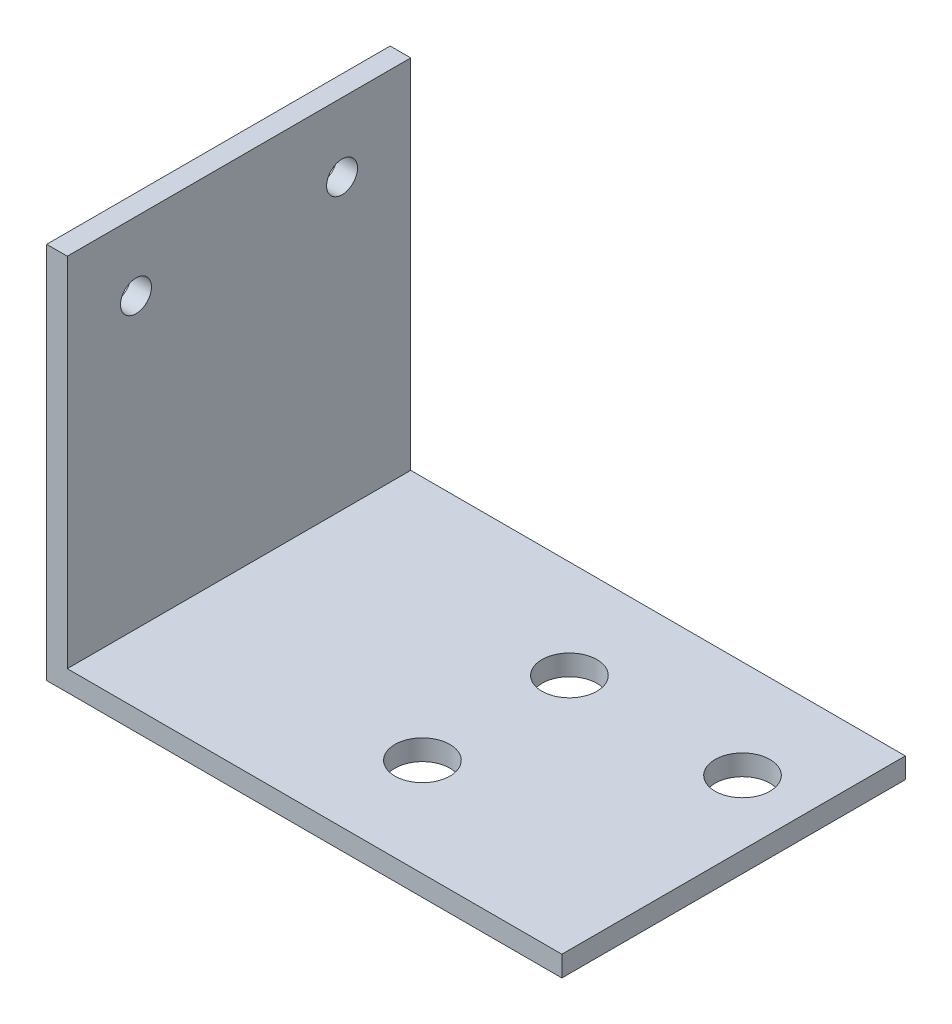
SolidWorks part; units mm, degrees
material "PBT Общее назначение"
ref_plane "Спереди" through (0, 0, 0) normal (0, 0, 1) x (1, 0, 0)
ref_plane "Сверху" through (0, 0, 0) normal (0, 1, 0) x (1, 0, 0)
ref_plane "Справа" through (0, 0, 0) normal (1, 0, 0) x (0, 0, -1)
sketch "Эскиз1" plane through (0, 0, 0) normal (0, 0, 1) x (1, 0, 0)
  line L0 (0, 0) -> (75, 0)
  line L1 (75, 0) -> (75, 3)
  line L2 (75, 3) -> (3, 3)
  line L3 (3, 3) -> (3, 55)
  line L4 (3, 55) -> (0, 55)
  line L5 (0, 55) -> (0, 0)
  dimension "D1" = 3
  dimension "D2" = 3
  dimension "D3" = 75
  dimension "D4" = 55
extrude "Бобышка-Вытянуть1" add sketch "Эскиз1" along normal blind 50
sketch "Эскиз2" plane through (0, 0, 0) normal (-1, 0, 0) x (0, 0, 1)
  line L0 (25, 55) -> (25, 0) construction
  line L1 (50, 55) -> (0, 55) construction
  line L2 (50, 0) -> (0, 0) construction
sketch "Эскиз3" plane through (0, 3, 0) normal (0, 1, 0) x (1, 0, 0)
  line L4 (66.75, -39.75) -> (66.75, -38.75)
  line L5 (66.75, -38.75) -> (39.25, -38.75)
  line L6 (39.25, -38.75) -> (39.25, -39.75)
  line L7 (39.25, -39.75) -> (66.75, -39.75)
  line L8 (66.75, -39.75) -> (66.75, -38.75)
  line L9 (66.75, -38.75) -> (39.25, -38.75)
  line L10 (39.25, -38.75) -> (39.25, -39.75)
  line L11 (39.25, -39.75) -> (66.75, -39.75)
  line L12 (66.75, -10.25) -> (39.25, -10.25)
  line L13 (66.75, -11.25) -> (66.75, -10.25)
  line L14 (39.25, -11.25) -> (66.75, -11.25)
  line L15 (39.25, -10.25) -> (39.25, -11.25)
  line L16 (66.75, -10.25) -> (39.25, -10.25)
  line L17 (66.75, -11.25) -> (66.75, -10.25)
  line L18 (39.25, -11.25) -> (66.75, -11.25)
  line L19 (39.25, -10.25) -> (39.25, -11.25)
  circle A0 centre (23, 25) radius 1.55 construction
  circle A1 centre (40.4, -35.7) radius 2
  circle A2 centre (40.4, -35.7) radius 2
  circle A3 centre (40.4, -14.3) radius 2
  circle A4 centre (40.4, -14.3) radius 2
  circle A7 centre (53, -32) radius 1
  circle A8 centre (53, -32) radius 1
  circle A9 centre (53, -18) radius 1
  circle A10 centre (53, -18) radius 1
  circle A11 centre (23, 25) radius 1.55
  circle A12 centre (23, -70) radius 1.55 construction
  circle A13 centre (23, -70) radius 1.55
  dimension "D1" = 0
  dimension "D2" = 0
  dimension "D4" = 0
  dimension "D5" = 0
  dimension "D6" = 0
  dimension "D7" = 0
sketch "Эскиз6" plane through (0, 3, 0) normal (0, 1, 0) x (1, 0, 0)
  circle A5 centre (40.4, -14.3) radius 2
  circle A6 centre (40.4, -14.3) radius 2
  circle A7 centre (40.4, -35.7) radius 2
  circle A8 centre (40.4, -35.7) radius 2
  dimension "D3" = 0
  dimension "D4" = 0
extrude "Вырез-Вытянуть2" cut sketch "Эскиз6" against normal through all
sketch "Sketch1" plane through (0, 3, 0) normal (0, 1, 0) x (1, 0, 0)
  circle A0 centre (65.6, -14.3) radius 2 construction
  circle A1 centre (65.6, -14.3) radius 2
extrude "Cut-Extrude1" cut sketch "Sketch1" against normal through all
sketch "Sketch2" plane through (0, 3, 0) normal (0, 1, 0) x (1, 0, 0)
  circle A0 centre (40.4, -14.3) radius 4
  circle A1 centre (65.6, -14.3) radius 4
  circle A2 centre (40.4, -35.7) radius 4
  dimension "D1" = 8
  dimension "D2" = 8
  dimension "D3" = 8
extrude "Cut-Extrude2" cut sketch "Sketch2" against normal through all
sketch "Sketch3" plane through (0, 3, 0) normal (0, 1, 0) x (1, 0, 0)
  line L0 (65.6, -14.3) -> (40.4, -14.3) construction
  line L1 (40.4, -14.3) -> (40.4, -35.7) construction
ref_plane "Отв вдоль" through (0, 0, 14.3) normal (0, 0, -1) x (-1, 0, 0)
ref_plane "Отв поп" through (40.4, 0, 0) normal (-1, 0, 0) x (0, 0, 1)
sketch "Sketch4" plane through (0, 0, 0) normal (-1, 0, 0) x (0, 0, 1)
  line L0 (0, 45) -> (50, 45) construction
  line L1 (0, 55) -> (0, 0) construction
  line L2 (50, 55) -> (50, 0) construction
  line L3 (50, 55) -> (0, 55) construction
  circle A0 centre (10, 45) radius 2.25
  circle A1 centre (40, 45) radius 2.25
  dimension "D2" = 4.5
  dimension "D3" = 4.5
  dimension "D4" = 10
  dimension "D5" = 10
  dimension "D1" = 10
extrude "Cut-Extrude3" cut sketch "Sketch4" against normal through all
